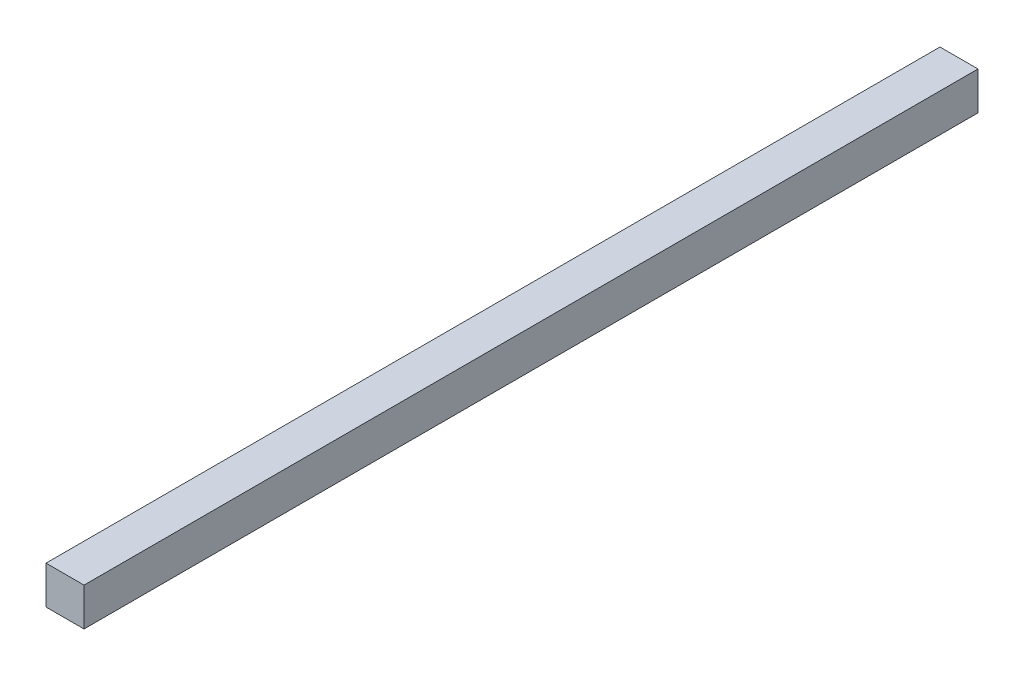
SolidWorks part; units mm, degrees
ref_plane "Front Plane" through (0, 0, 0) normal (0, 0, 1) x (1, 0, 0)
ref_plane "Top Plane" through (0, 0, 0) normal (0, 1, 0) x (1, 0, 0)
ref_plane "Right Plane" through (0, 0, 0) normal (1, 0, 0) x (0, 0, -1)
sketch "Sketch1" plane through (0, 0, 0) normal (0, 0, 1) x (1, 0, 0)
  line L1 (12.7, -12.7) -> (-12.7, -12.7)
  line L2 (12.7, -12.7) -> (12.7, 12.7)
  line L3 (12.7, 12.7) -> (-12.7, 12.7)
  line L4 (-12.7, -12.7) -> (-12.7, 12.7)
  line L5 (12.7, -12.7) -> (-12.7, 12.7) construction
  line L6 (12.7, 12.7) -> (-12.7, -12.7) construction
  point P0 (0, 0)
  dimension "D1" = 25.4
extrude "Boss-Extrude1" add sketch "Sketch1" along normal blind 596.9
sketch "Sketch2" plane through (12.7, 0, 0) normal (1, 0, 0) x (0, 0, -1)
  line L0 (-596.9, 0) -> (0, 0) construction
  line L1 (-596.9, -12.7) -> (-596.9, 12.7) construction
  circle A0 centre (15.24, 0) radius 6.35
  circle A1 centre (-10.16, 0) radius 6.35
  circle A2 centre (-35.56, 0) radius 6.35
  circle A3 centre (-60.96, 0) radius 6.35
  circle A4 centre (-86.36, 0) radius 6.35
  circle A5 centre (-111.76, 0) radius 6.35
  circle A6 centre (-137.16, 0) radius 6.35
  circle A7 centre (-162.56, 0) radius 6.35
  circle A8 centre (-187.96, 0) radius 6.35
  circle A9 centre (-213.36, 0) radius 6.35
  circle A10 centre (-238.76, 0) radius 6.35
  circle A11 centre (-264.16, 0) radius 6.35
  circle A12 centre (-289.56, 0) radius 6.35
  circle A13 centre (-314.96, 0) radius 6.35
  circle A14 centre (-340.36, 0) radius 6.35
  circle A15 centre (-365.76, 0) radius 6.35
  circle A16 centre (-391.16, 0) radius 6.35
  circle A17 centre (-416.56, 0) radius 6.35
  circle A18 centre (-441.96, 0) radius 6.35
  circle A19 centre (-492.76, 0) radius 6.35
  circle A20 centre (-467.36, 0) radius 6.35
  circle A21 centre (-518.16, 0) radius 6.35
  circle A22 centre (-543.56, 0) radius 6.35
  circle A23 centre (-568.96, 0) radius 6.35
  circle A24 centre (-594.36, 0) radius 6.35
  point P55 (0, 0)
  point P56 (-65.0344, 0)
  point P58 (-384.7715, 31.3158)
  dimension "D1" = 12.7
  dimension "D2" = 25.4
  dimension "D3" = 25.4
  dimension "D4" = 25.4
  dimension "D5" = 25.4
  dimension "D6" = 25.4
  dimension "D7" = 25.4
  dimension "D8" = 25.4
  dimension "D9" = 2.54
  dimension "D10" = 25.4
  dimension "D11" = 25.4
  dimension "D12" = 25.4
  dimension "D13" = 25.4
  dimension "D14" = 25.4
  dimension "D15" = 25.4
  dimension "D16" = 25.4
  dimension "D17" = 25.4
  dimension "D18" = 25.4
  dimension "D19" = 25.4
  dimension "D20" = 25.4
  dimension "D21" = 25.4
  dimension "D22" = 25.4
  dimension "D23" = 25.4
  dimension "D24" = 25.4
  dimension "D25" = 25.4
  dimension "D26" = 25.4
